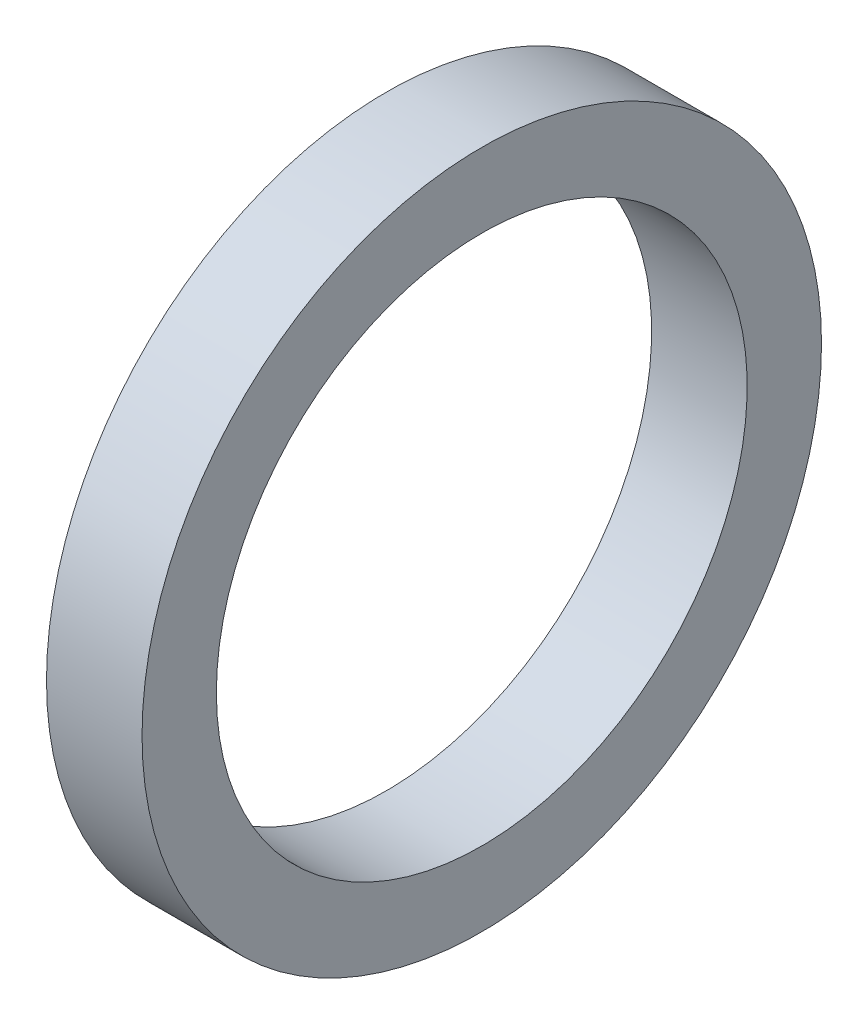
SolidWorks part; units mm, degrees
ref_plane "Ebene vorne" through (0, 0, 0) normal (0, 0, 1) x (1, 0, 0)
ref_plane "Ebene oben" through (0, 0, 0) normal (0, 1, 0) x (1, 0, 0)
ref_plane "Ebene rechts" through (0, 0, 0) normal (1, 0, 0) x (0, 0, -1)
sketch "Skizze1" plane through (0, 0, 0) normal (0, 0, 1) x (1, 0, 0)
  line L0 (-2.5, 12.5) -> (2, 12.5)
  line L1 (2, 12.5) -> (2, 16)
  line L2 (2, 16) -> (-2.5, 16)
  line L3 (-2.5, 16) -> (-2.5, 12.5)
  line L4 (-5.6383, 0) -> (31.3756, 0) construction
  dimension "D1" = 16
  dimension "D2" = 12.5
  dimension "D3" = 4.5
  dimension "D4" = 2
revolve "Rotation1" add sketch "Skizze1" angle 360 about L4
